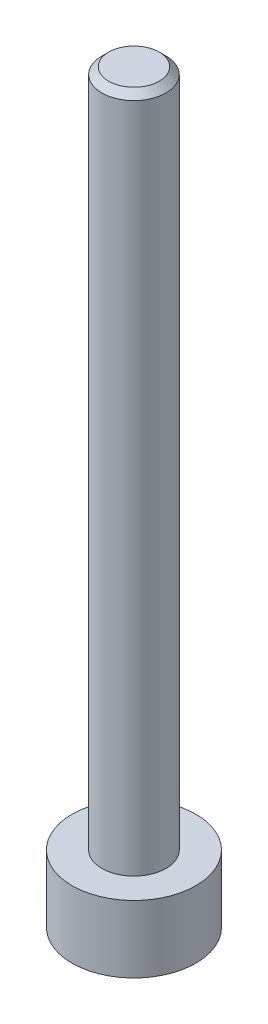
SolidWorks part; units mm, degrees
ref_plane "Front Plane" through (0, 0, 0) normal (0, 0, 1) x (1, 0, 0)
ref_plane "Top Plane" through (0, 0, 0) normal (0, 1, 0) x (1, 0, 0)
ref_plane "Right Plane" through (0, 0, 0) normal (1, 0, 0) x (0, 0, -1)
sketch "Sketch1" plane through (0, 0, 0) normal (0, 1, 0) x (1, 0, 0)
  circle A0 centre (0, 0) radius 1.825
  dimension "D1" = 3.65
extrude "Boss-Extrude1" add sketch "Sketch1" along normal blind 1.98
sketch "Sketch2" plane through (0, 1.98, 0) normal (0, 1, 0) x (1, 0, 0)
  circle A0 centre (0, 0) radius 0.945
  dimension "D1" = 1.89
extrude "Boss-Extrude2" add sketch "Sketch2" along normal blind 20
sketch "Sketch3" plane through (0, 0, 0) normal (0, -1, 0) x (1, 0, 0)
  line L1 (0.459, -0.795) -> (0.918, 0)
  line L2 (0.918, 0) -> (0.459, 0.795)
  line L3 (0.459, 0.795) -> (-0.459, 0.795)
  line L4 (-0.459, 0.795) -> (-0.918, 0)
  line L5 (-0.918, 0) -> (-0.459, -0.795)
  line L6 (-0.459, -0.795) -> (0.459, -0.795)
  circle A0 centre (0, 0) radius 0.795 construction
  dimension "D1" = 1.59
extrude "Cut-Extrude1" cut sketch "Sketch3" against normal blind 1
chamfer "Chamfer1" distance 0.2 angle 45 1 edges at (0, 21.98, 0.945)
